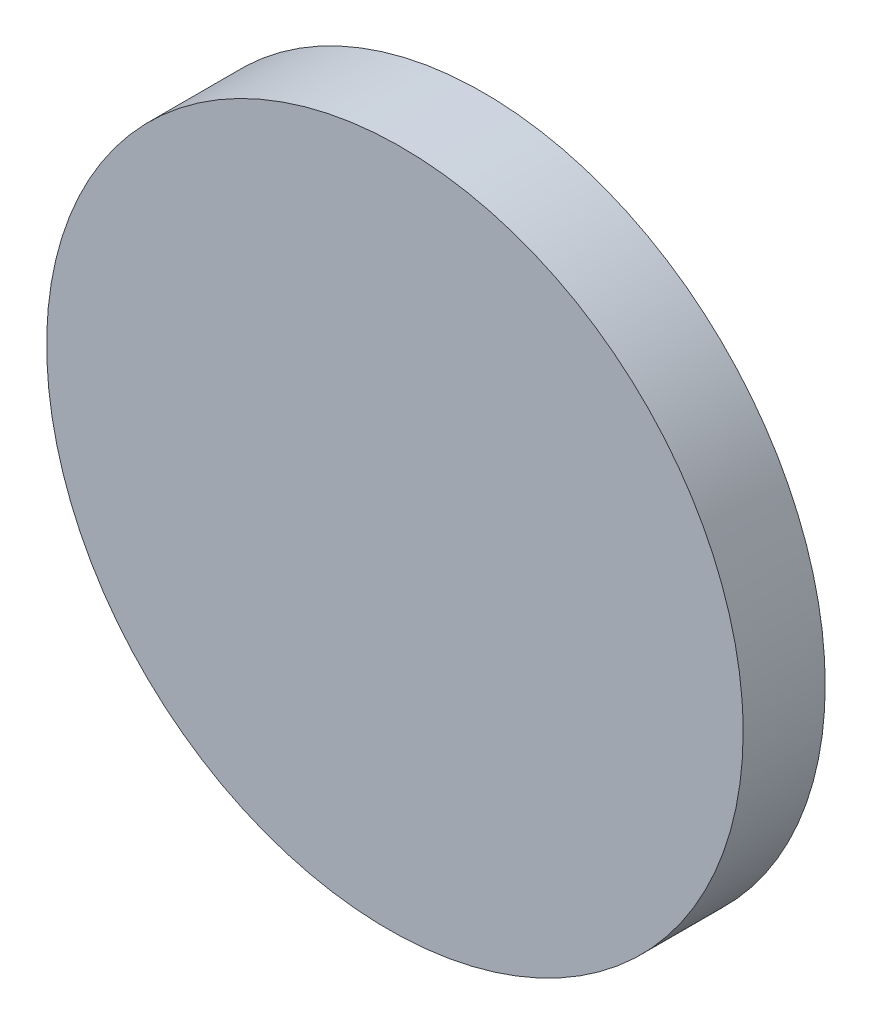
SolidWorks part; units mm, degrees
ref_plane "前视基准面" through (0, 0, 0) normal (0, 0, 1) x (1, 0, 0)
ref_plane "上视基准面" through (0, 0, 0) normal (0, 1, 0) x (1, 0, 0)
ref_plane "右视基准面" through (0, 0, 0) normal (1, 0, 0) x (0, 0, -1)
sketch "草图1" plane through (0, 0, 0) normal (0, 0, 1) x (1, 0, 0)
  circle A0 centre (0, 0) radius 12.5
extrude "凸台-拉伸1" add sketch "草图1" along normal blind 10
sketch "草图2" plane through (0, 0, 0) normal (0, 1, 0) x (1, 0, 0)
  line L0 (12.5, -3) -> (-16.6373, -3.534)
  line L1 (12.5, -10) -> (12.5, 0) construction
  line L2 (-16.6373, -3.534) -> (-16.6373, -14.4719)
  line L3 (-16.6373, -14.4719) -> (17.7716, -14.4719)
  line L4 (17.7716, -14.4719) -> (17.7716, -3)
  line L5 (17.7716, -3) -> (12.5, -3)
  line L6 (12.5, 0) -> (-12.5, 0) construction
  dimension "D1" = 1.05
  dimension "D2" = 3
extrude "切除-拉伸1" cut sketch "草图2" against normal mid plane 50
